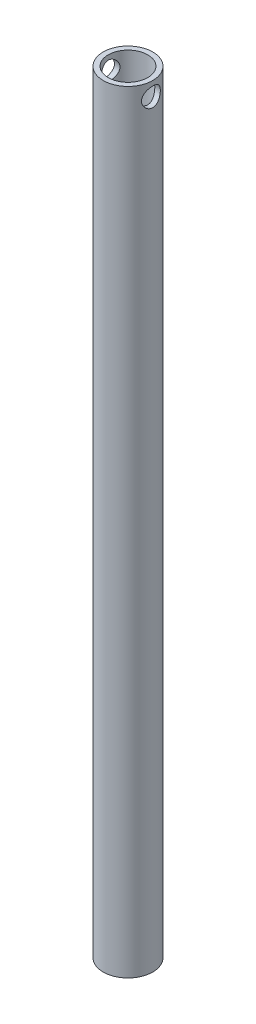
SolidWorks part; units mm, degrees
material "6061-T6 (SS)"
ref_plane "Front Plane" through (0, 0, 0) normal (0, 0, 1) x (1, 0, 0)
ref_plane "Top Plane" through (0, 0, 0) normal (0, 1, 0) x (1, 0, 0)
ref_plane "Right Plane" through (0, 0, 0) normal (1, 0, 0) x (0, 0, -1)
sketch "Sketch1" plane through (0, 0, 0) normal (0, 1, 0) x (1, 0, 0)
  circle A0 centre (0, 0) radius 16.7005
  circle A1 centre (0, 0) radius 13.335
  dimension "D1" = 33.401
  dimension "D2" = 26.67
extrude "Boss-Extrude1" add sketch "Sketch1" along normal blind 520.7
sketch "Sketch2" plane through (0, 0, 0) normal (1, 0, 0) x (0, 0, -1)
  line L0 (16.7005, 520.7) -> (-16.7005, 520.7) construction
  line L1 (0, 18.3705) -> (0, -18.3705) construction
  circle A0 centre (0, 511.175) radius 6.35
  dimension "D1" = 12.7
  dimension "D2" = 9.525
extrude "Cut-Extrude1" cut sketch "Sketch2" against normal through all both and the other way through all
